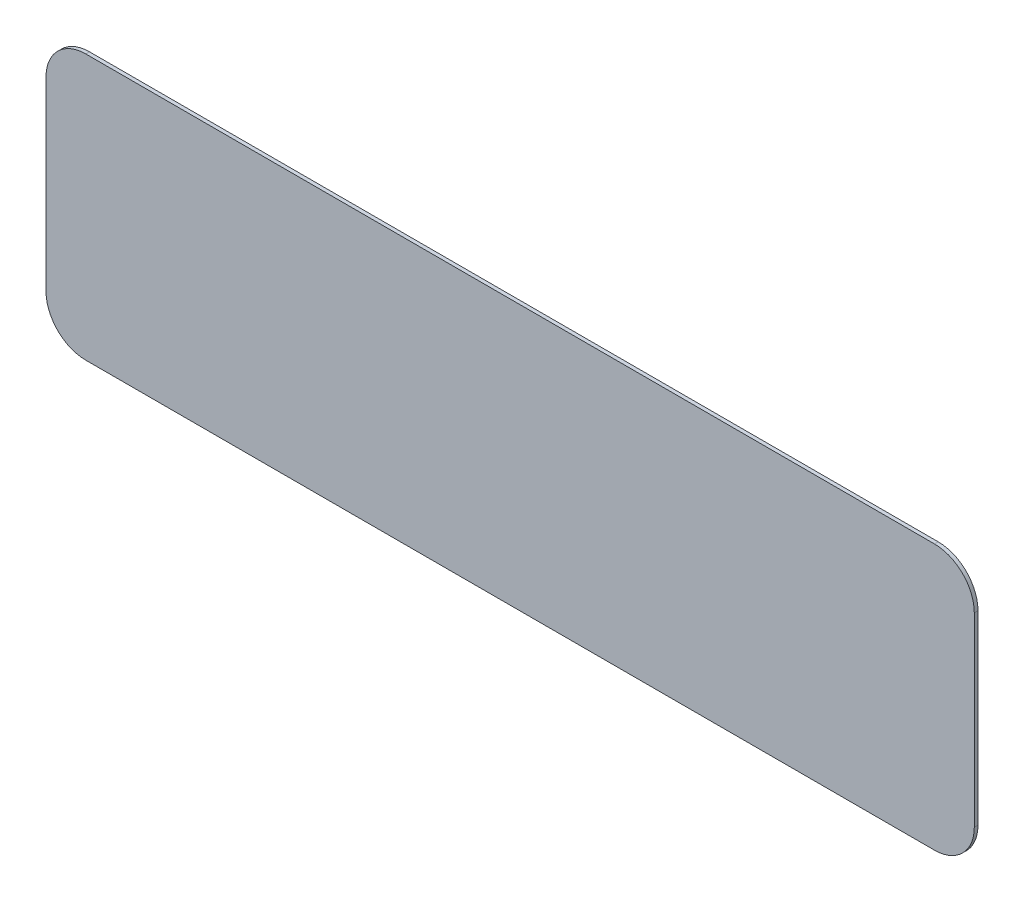
SolidWorks part; units mm, degrees
ref_plane "Front Plane" through (0, 0, 0) normal (0, 0, 1) x (1, 0, 0)
ref_plane "Top Plane" through (0, 0, 0) normal (0, 1, 0) x (1, 0, 0)
ref_plane "Right Plane" through (0, 0, 0) normal (1, 0, 0) x (0, 0, -1)
sketch "Sketch1" plane through (0, 0, 0) normal (0, 0, 1) x (1, 0, 0)
  line L1 (-20.32, -6.35) -> (20.32, -6.35)
  line L2 (-22.225, -4.445) -> (-22.225, 4.445)
  line L3 (-20.32, 6.35) -> (20.32, 6.35)
  line L4 (22.225, -4.445) -> (22.225, 4.445)
  line L5 (-22.225, -6.35) -> (22.225, 6.35) construction
  line L6 (-22.225, 6.35) -> (22.225, -6.35) construction
  arc A0 (20.32, 6.35) -> (22.225, 4.445) centre (20.32, 4.445) cw
  arc A1 (20.32, -6.35) -> (22.225, -4.445) centre (20.32, -4.445) ccw
  arc A2 (-20.32, -6.35) -> (-22.225, -4.445) centre (-20.32, -4.445) cw
  arc A3 (-22.225, 4.445) -> (-20.32, 6.35) centre (-20.32, 4.445) cw
  point P0 (0, 0)
  dimension "D3" = 1.905
  dimension "D1" = 44.45
  dimension "D2" = 12.7
extrude "Boss-Extrude1" add sketch "Sketch1" along normal blind 0.1778
